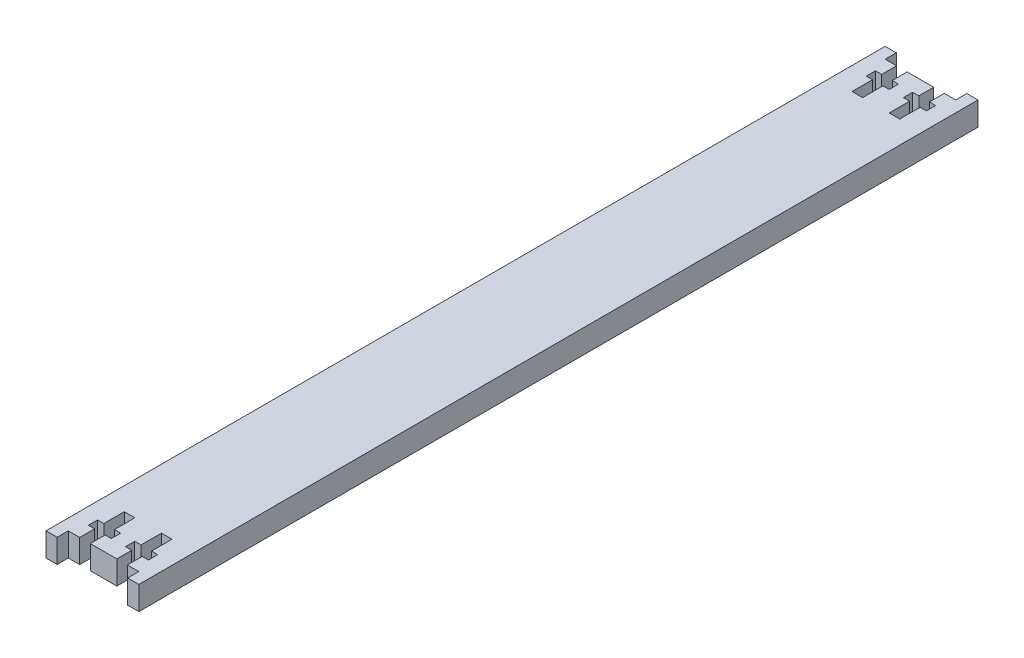
SolidWorks part; units mm, degrees
ref_plane "Front Plane" through (0, 0, 0) normal (0, 0, 1) x (1, 0, 0)
ref_plane "Top Plane" through (0, 0, 0) normal (0, 1, 0) x (1, 0, 0)
ref_plane "Right Plane" through (0, 0, 0) normal (1, 0, 0) x (0, 0, -1)
sketch "Sketch1" plane through (0, 0, 0) normal (0, 1, 0) x (1, 0, 0)
  line L0 (8.9224, 220) -> (8.9224, 216)
  line L1 (3, 0) -> (6.0776, 0)
  line L2 (0, 0) -> (0, 220)
  line L3 (3, 220) -> (6.0776, 220)
  line L4 (25, 0) -> (25, 220)
  line L5 (12.5, 220) -> (12.5, 0) construction
  line L6 (0, 110) -> (25, 110) construction
  line L7 (8.9224, 216) -> (10.6, 216)
  line L8 (10.6, 216) -> (10.6, 213.5)
  line L9 (10.6, 213.5) -> (8.9224, 213.5)
  line L10 (8.9224, 213.5) -> (8.9224, 208)
  line L11 (8.9224, 208) -> (6.0776, 208)
  line L12 (6.0776, 208) -> (6.0776, 213.5)
  line L13 (6.0776, 213.5) -> (4.4, 213.5)
  line L14 (4.4, 213.5) -> (4.4, 216)
  line L15 (4.4, 216) -> (6.0776, 216)
  line L16 (6.0776, 216) -> (6.0776, 220)
  line L17 (14.4, 216) -> (14.4, 213.5)
  line L18 (18.9224, 216) -> (18.9224, 220)
  line L19 (20.6, 216) -> (18.9224, 216)
  line L20 (20.6, 213.5) -> (20.6, 216)
  line L21 (18.9224, 213.5) -> (20.6, 213.5)
  line L22 (18.9224, 208) -> (18.9224, 213.5)
  line L23 (16.0776, 208) -> (18.9224, 208)
  line L24 (16.0776, 213.5) -> (16.0776, 208)
  line L25 (14.4, 213.5) -> (16.0776, 213.5)
  line L26 (16.0776, 216) -> (14.4, 216)
  line L27 (16.0776, 220) -> (16.0776, 216)
  line L28 (16.0776, 0) -> (16.0776, 4)
  line L29 (16.0776, 4) -> (14.4, 4)
  line L30 (14.4, 6.5) -> (16.0776, 6.5)
  line L31 (16.0776, 6.5) -> (16.0776, 12)
  line L32 (16.0776, 12) -> (18.9224, 12)
  line L33 (18.9224, 12) -> (18.9224, 6.5)
  line L34 (18.9224, 6.5) -> (20.6, 6.5)
  line L35 (20.6, 6.5) -> (20.6, 4)
  line L36 (20.6, 4) -> (18.9224, 4)
  line L37 (18.9224, 4) -> (18.9224, 0)
  line L38 (14.4, 4) -> (14.4, 6.5)
  line L39 (10.6, 4) -> (10.6, 6.5)
  line L40 (6.0776, 4) -> (6.0776, 0)
  line L41 (4.4, 4) -> (6.0776, 4)
  line L42 (4.4, 6.5) -> (4.4, 4)
  line L43 (6.0776, 6.5) -> (4.4, 6.5)
  line L44 (6.0776, 12) -> (6.0776, 6.5)
  line L45 (8.9224, 12) -> (6.0776, 12)
  line L46 (8.9224, 6.5) -> (8.9224, 12)
  line L47 (10.6, 6.5) -> (8.9224, 6.5)
  line L48 (8.9224, 4) -> (10.6, 4)
  line L49 (8.9224, 0) -> (8.9224, 4)
  line L50 (8.9224, 220) -> (16.0776, 220)
  line L51 (18.9224, 220) -> (22, 220)
  line L52 (8.9224, 0) -> (16.0776, 0)
  line L53 (18.9224, 0) -> (22, 0)
  line L54 (0, 220) -> (0, 223)
  line L55 (0, 223) -> (3, 223)
  line L56 (3, 223) -> (3, 220)
  line L57 (22, 223) -> (22, 220)
  line L58 (25, 223) -> (22, 223)
  line L59 (25, 220) -> (25, 223)
  line L60 (25, 0) -> (25, -3)
  line L61 (25, -3) -> (22, -3)
  line L62 (22, -3) -> (22, 0)
  line L63 (3, -3) -> (3, 0)
  line L64 (0, -3) -> (3, -3)
  line L65 (0, 0) -> (0, -3)
  point P54 (7.5, 208)
  point P57 (12.5, 110)
  point P66 (17.5, 208)
  point P160 (12.5, 110)
  dimension "D1" = 220
  dimension "D2" = 25
  dimension "D3" = 2.8448
  dimension "D4" = 2.5
  dimension "D5" = 12
  dimension "D6" = 4
  dimension "D7" = 6.2
  dimension "D8" = 10
  dimension "D9" = 3
extrude "Boss-Extrude1" add sketch "Sketch1" along normal blind 6.35
